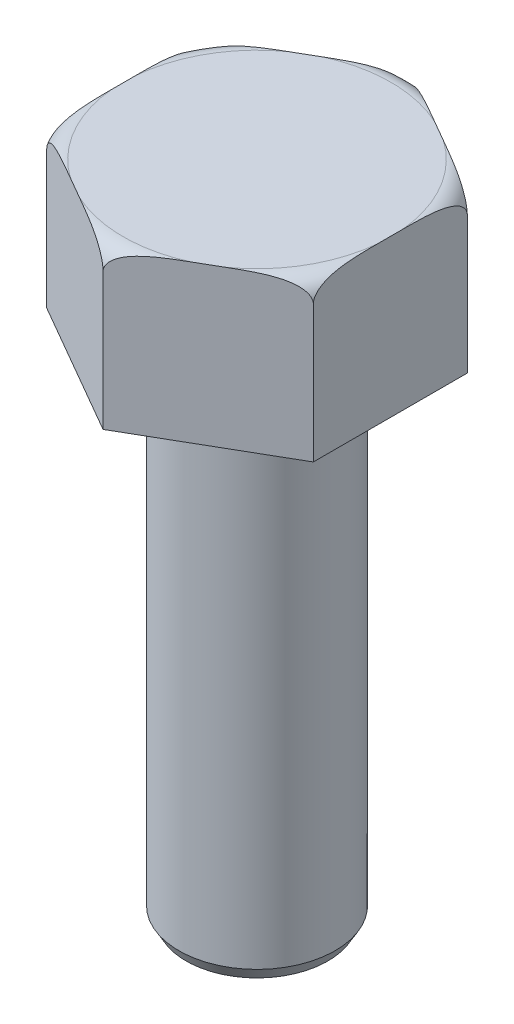
SolidWorks part; units mm, degrees
ref_plane "Front Plane" through (0, 0, 0) normal (0, 0, 1) x (1, 0, 0)
ref_plane "Top Plane" through (0, 0, 0) normal (0, 1, 0) x (1, 0, 0)
ref_plane "Right Plane" through (0, 0, 0) normal (1, 0, 0) x (0, 0, -1)
sketch "Sketch1" plane through (0, 0, 0) normal (0, 1, 0) x (1, 0, 0)
  line L1 (0, -15.5812) -> (13.4937, -7.7906)
  line L2 (13.4937, -7.7906) -> (13.4937, 7.7906)
  line L3 (13.4937, 7.7906) -> (0, 15.5812)
  line L4 (0, 15.5812) -> (-13.4938, 7.7906)
  line L5 (-13.4938, 7.7906) -> (-13.4938, -7.7906)
  line L6 (-13.4938, -7.7906) -> (0, -15.5812)
  circle A0 centre (0, 0) radius 13.4938 construction
  dimension "D1" = 26.9875
extrude "Boss-Extrude1" add sketch "Sketch1" along normal blind 15.875
sketch "Sketch2" plane through (0, 0, 0) normal (1, 0, 0) x (0, 0, -1)
  line L0 (0, 15.875) -> (0, 0) construction
  line L1 (-7.7906, 15.875) -> (7.7906, 15.875) construction
  line L4 (13.5492, 15.875) -> (15.5812, 15.875)
  line L5 (15.5812, 15.875) -> (15.5812, 13.843)
  arc A0 (13.5492, 15.875) -> (15.5812, 13.843) centre (13.5492, 13.843) cw
  point P11 (15.5812, 15.875)
  dimension "D1" = 2.032
revolve "Cut-Revolve1" cut sketch "Sketch2" angle 360 about L0
sketch "Sketch6" plane through (0, 0, 0) normal (0, -1, 0) x (1, 0, 0)
  circle A0 centre (0, 0) radius 7.9121
  dimension "D1" = 15.8242
extrude "Boss-Extrude2" add sketch "Sketch6" along normal blind 50.8
chamfer "Chamfer1" distance 1.27 angle 30 1 edges at (0, -50.8, -7.9121)
